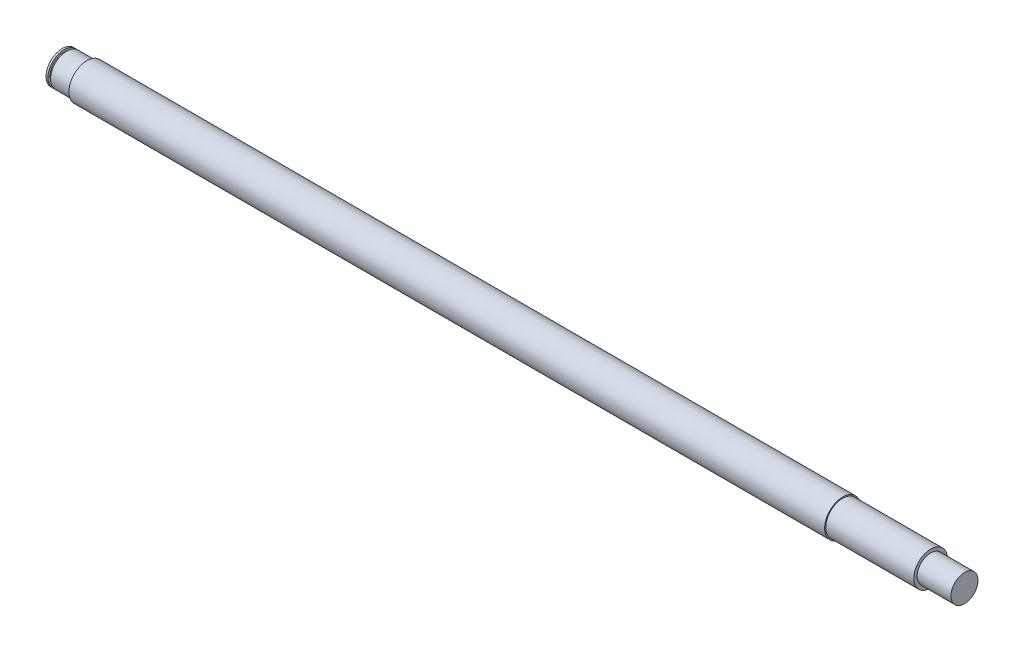
SolidWorks part; units mm, degrees
material "合金钢"
ref_plane "前视基准面" through (0, 0, 0) normal (0, 0, 1) x (1, 0, 0)
ref_plane "上视基准面" through (0, 0, 0) normal (0, 1, 0) x (1, 0, 0)
ref_plane "右视基准面" through (0, 0, 0) normal (1, 0, 0) x (0, 0, -1)
sketch "草图1" plane through (0, 0, 0) normal (0, 0, 1) x (1, 0, 0)
  line L0 (-271.9228, 0) -> (581.4456, 0) construction
  line L1 (0, 0) -> (0, 7.15)
  line L2 (0, 7.15) -> (0.85, 7.15)
  line L3 (0.85, 7.15) -> (0.85, 6.15)
  line L4 (0.85, 6.15) -> (2, 6.15)
  line L5 (2, 6.15) -> (2, 7.15)
  line L6 (2, 7.15) -> (11, 7.15)
  line L7 (11, 7.15) -> (11, 8)
  line L8 (11, 8) -> (346, 8)
  line L9 (346, 8) -> (346, 7.5)
  line L10 (346, 7.5) -> (385, 7.5)
  line L11 (385, 7.5) -> (385, 6)
  line L12 (385, 6) -> (400, 6)
  line L13 (400, 6) -> (400, 0)
  line L14 (400, 0) -> (0, 0)
  dimension "D1" = 400
  dimension "D2" = 14.3
  dimension "D3" = 1.15
  dimension "D4" = 9
  dimension "D5" = 11
  dimension "D6" = 1
  dimension "D7" = 16
  dimension "D8" = 15
  dimension "D9" = 12
  dimension "D10" = 15
  dimension "D11" = 39
revolve "旋转1" add sketch "草图1" angle 360 about L0
